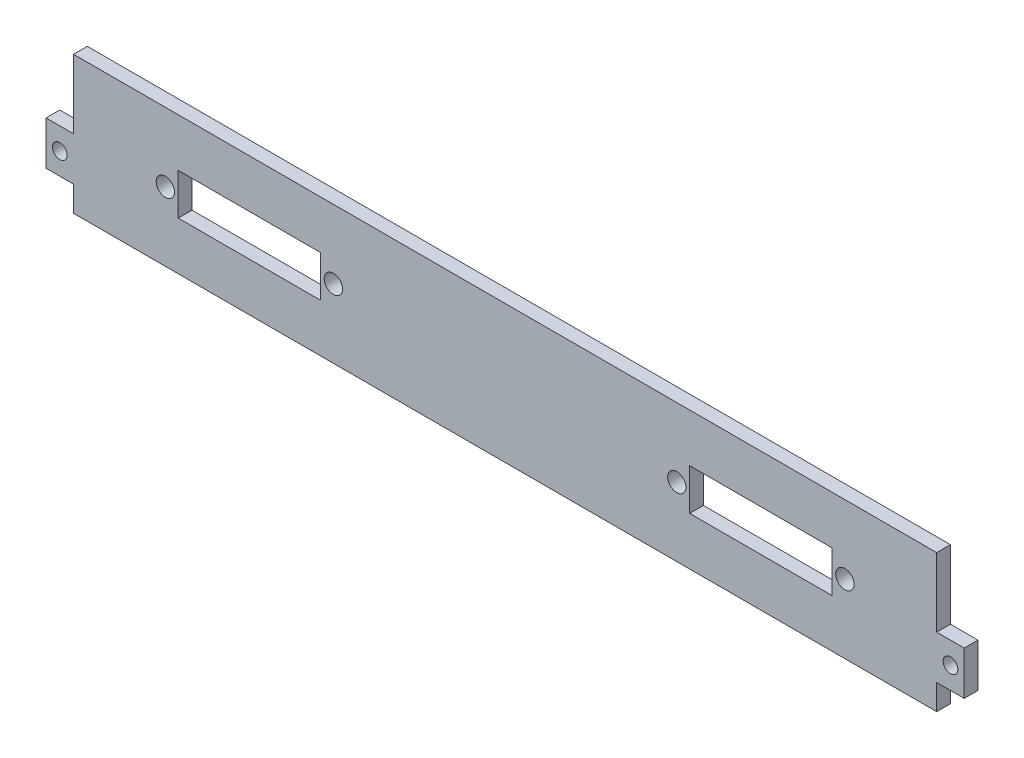
SolidWorks part; units mm, degrees
material "Balsa"
ref_plane "Plano frontal" through (0, 0, 0) normal (0, 0, 1) x (1, 0, 0)
ref_plane "Plano superior" through (0, 0, 0) normal (0, 1, 0) x (1, 0, 0)
ref_plane "Plano direito" through (0, 0, 0) normal (1, 0, 0) x (0, 0, -1)
sketch "Esboço1" plane through (0, 0, 0) normal (0, 0, 1) x (1, 0, 0)
  line L0 (-94, -9.5) -> (-94, -15)
  line L1 (-94, 15) -> (94, 15)
  line L2 (-94, 15) -> (-94, 0)
  line L3 (-94, -15) -> (94, -15)
  line L4 (94, 15) -> (94, 0)
  line L5 (-94, 15) -> (94, -15) construction
  line L6 (-94, -15) -> (94, 15) construction
  line L7 (-94, 0) -> (-100, 0)
  line L8 (0, 15) -> (0, -15) construction
  line L9 (-94, -9.5) -> (-100, -9.5)
  line L10 (-100, 0) -> (-100, -9.5)
  line L11 (94, 0) -> (100, 0)
  line L12 (94, -9.5) -> (100, -9.5)
  line L13 (100, 0) -> (100, -9.5)
  line L14 (94, -9.5) -> (94, -15)
  line L15 (-100, 0) -> (-94, -9.5) construction
  line L16 (-74, 0) -> (-37.4, 0) construction
  line L17 (71.2, -4.5) -> (40.2, 4.5) construction
  line L18 (-71.2, 4.5) -> (-40.2, 4.5)
  line L19 (-71.2, 4.5) -> (-71.2, -4.5)
  line L20 (-71.2, -4.5) -> (-40.2, -4.5)
  line L21 (-40.2, 4.5) -> (-40.2, -4.5)
  line L22 (-71.2, 4.5) -> (-40.2, -4.5) construction
  line L23 (-71.2, -4.5) -> (-40.2, 4.5) construction
  line L24 (71.2, 4.5) -> (40.2, -4.5) construction
  line L25 (74, 0) -> (37.4, 0) construction
  line L26 (40.2, 4.5) -> (40.2, -4.5)
  line L27 (71.2, -4.5) -> (40.2, -4.5)
  line L28 (71.2, 4.5) -> (71.2, -4.5)
  line L29 (71.2, 4.5) -> (40.2, 4.5)
  circle A0 centre (-97, -4.75) radius 1.6
  circle A1 centre (97, -4.75) radius 1.6
  circle A2 centre (-74, 0) radius 2
  circle A3 centre (-37.4, 0) radius 2
  circle A4 centre (37.4, 0) radius 2
  circle A5 centre (74, 0) radius 2
  point P0 (0, 0)
  point P24 (-55.7, 0)
  point P33 (0, 0)
  point P38 (55.7, 0)
  dimension "D6" = 3.2
  dimension "D7" = 4
  dimension "D1" = 188
  dimension "D2" = 30
  dimension "D3" = 9.5
  dimension "D4" = 6
  dimension "D5" = 15
  dimension "D8" = 36.6
  dimension "D9" = 15
  dimension "D10" = 20
  dimension "D11" = 9
  dimension "D12" = 31
extrude "Ressalto-extrusão1" add sketch "Esboço1" along normal blind 3
